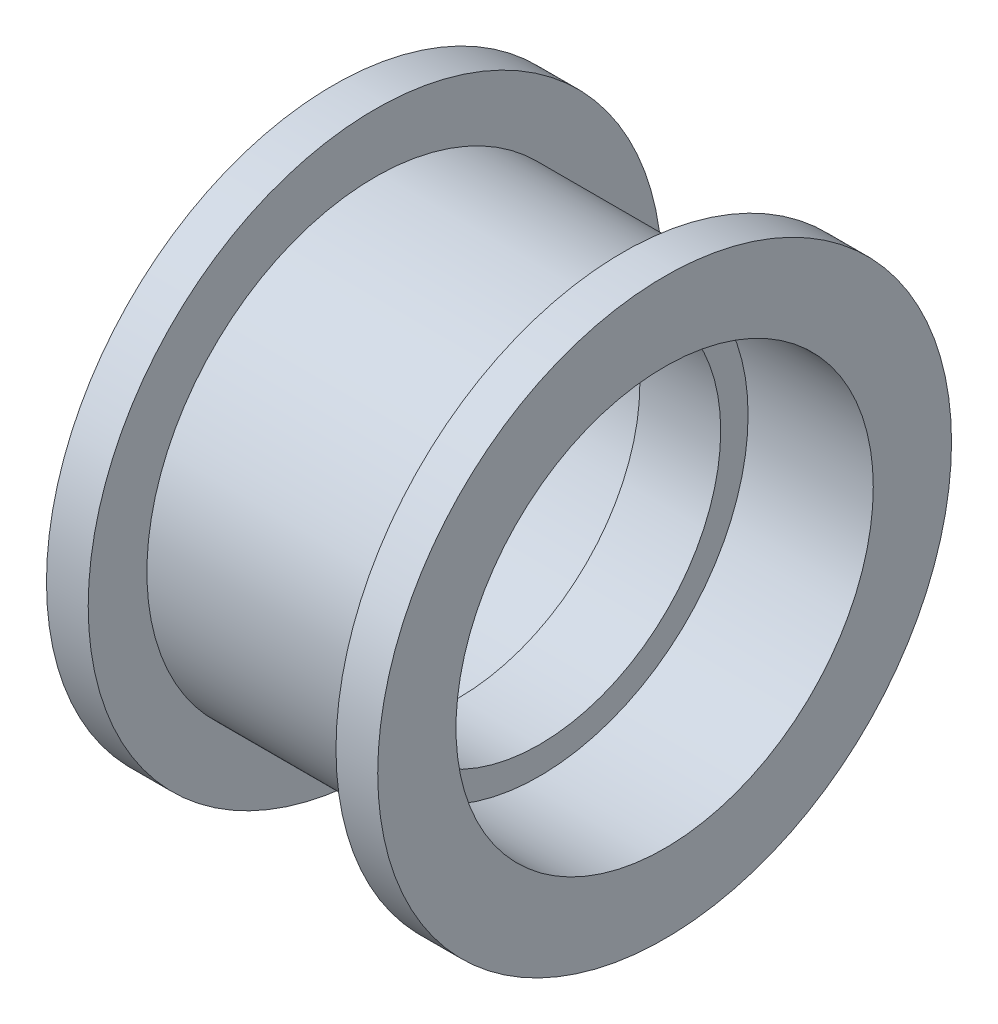
SolidWorks part; units mm, degrees
material "Delrin 2700 NC010, Low Viscosity Acetal Copolymer (SS)"
ref_plane "Front Plane" through (0, 0, 0) normal (0, 0, 1) x (1, 0, 0)
ref_plane "Top Plane" through (0, 0, 0) normal (0, 1, 0) x (1, 0, 0)
ref_plane "Right Plane" through (0, 0, 0) normal (1, 0, 0) x (0, 0, -1)
sketch "Sketch1" plane through (0, 0, 0) normal (0, 0, 1) x (1, 0, 0)
  line L0 (1.55, 6.95) -> (-1.55, 6.95)
  line L1 (-1.55, 6.95) -> (-1.55, 8)
  line L2 (-1.55, 8) -> (-6.35, 8)
  line L3 (-6.35, 8) -> (-6.35, 11)
  line L4 (-6.35, 11) -> (-4.75, 11)
  line L5 (-4.75, 8.75) -> (4.75, 8.75)
  line L6 (0, 8.75) -> (0, 6.95) construction
  line L7 (-4.75, 11) -> (-4.75, 8.75)
  line L8 (6.35, 8) -> (6.35, 11)
  line L9 (1.55, 8) -> (6.35, 8)
  line L10 (1.55, 6.95) -> (1.55, 8)
  line L11 (0, 0) -> (-12.6359, 0) construction
  line L12 (4.75, 11) -> (4.75, 8.75)
  line L13 (6.35, 11) -> (4.75, 11)
  dimension "D1" = 1.6
  dimension "8.64" = 13.9
  dimension "D2" = 16
  dimension "D3" = 17.5
  dimension "D4" = 3.1
  dimension "D5" = 22
  dimension "D6" = 12.7
revolve "Revolve1" add sketch "Sketch1" angle 360 about L11
ref_plane "Mid Idler Plane" through (0, 0, 0) normal (1, 0, 0) x (0, 0, -1)
